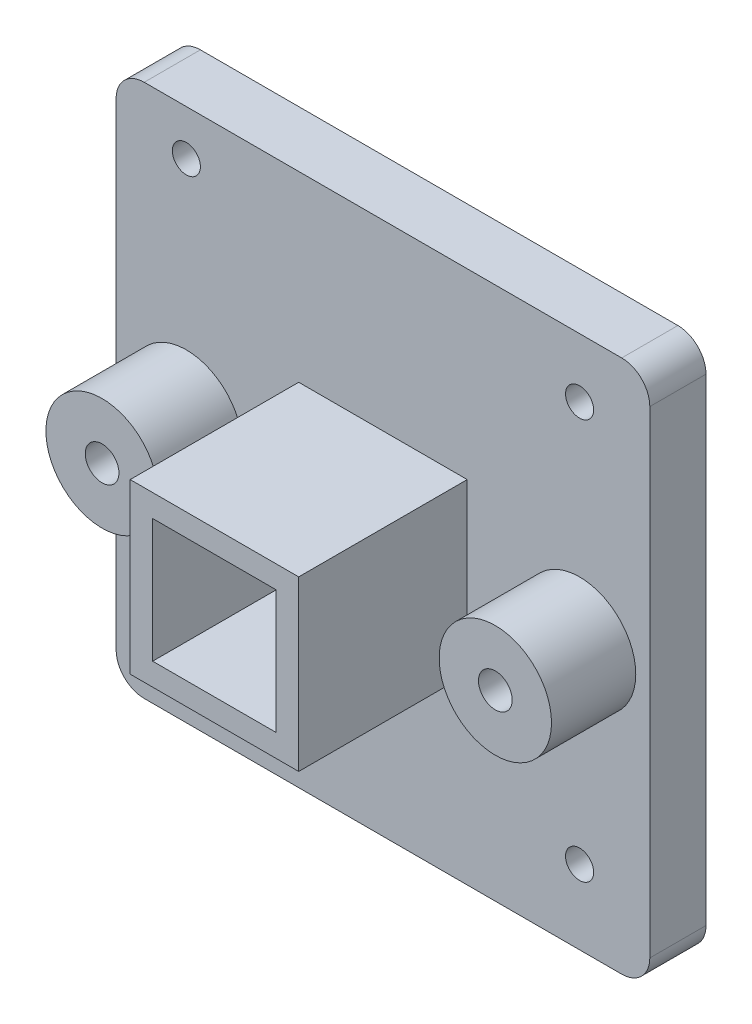
SolidWorks part; units mm, degrees
ref_plane "Front Plane" through (0, 0, 0) normal (0, 0, 1) x (1, 0, 0)
ref_plane "Top Plane" through (0, 0, 0) normal (0, 1, 0) x (1, 0, 0)
ref_plane "Right Plane" through (0, 0, 0) normal (1, 0, 0) x (0, 0, -1)
sketch "Sketch1" plane through (0, 0, 0) normal (0, 0, 1) x (1, 0, 0)
  line L1 (-22, -22) -> (22, -22)
  line L2 (-95, -95) -> (95, -95)
  line L3 (-95, -95) -> (-95, 95)
  line L4 (-95, 95) -> (95, 95)
  line L5 (95, -95) -> (95, 95)
  line L6 (-22, -22) -> (-22, 22)
  line L7 (-22, 22) -> (22, 22)
  line L8 (22, -22) -> (22, 22)
  circle A0 centre (-70, 0) radius 20
  circle A1 centre (70, 0) radius 20
  circle A2 centre (70, -68.5969) radius 5
  circle A3 centre (-70, -73.5969) radius 5
  circle A4 centre (70, 73.9364) radius 5
  circle A5 centre (-70, 78.9364) radius 5
  point P0 (0, 0)
  point P3 (0, 0)
  point P11 (0, 0)
  point P13 (0, 0)
  dimension "D4" = 44
  dimension "D3" = 44
  dimension "D1" = 190
  dimension "D2" = 190
extrude "Boss-Extrude2" add sketch "Sketch1" along normal blind 20
sketch "Sketch2" plane through (0, 0, 0) normal (0, 0, 1) x (1, 0, 0)
  circle A0 centre (-70, 0) radius 20
  circle A1 centre (70, 0) radius 20
  circle A2 centre (-70, 0) radius 6
  circle A3 centre (70, 0) radius 6
extrude "Boss-Extrude5" add sketch "Sketch2" along normal blind 50
sketch "Sketch4" plane through (0, 0, 0) normal (0, 0, 1) x (1, 0, 0)
  circle A0 centre (70, 0) radius 20
  circle A1 centre (-70, 0) radius 20
extrude "Boss-Extrude6" add sketch "Sketch4" along normal blind 3
fillet "Fillet1" radius 10 4 edges at (95, 95, 10) (-95, 95, 10) (-95, -95, 10) (95, -95, 10)
sketch "Sketch6" plane through (0, 0, 0) normal (0, 0, 1) x (1, 0, 0)
  line L0 (22, -22) -> (22, 22) construction
  line L1 (-22, -22) -> (22, -22)
  line L2 (-22, -22) -> (-22, 22)
  line L3 (-22, 22) -> (22, 22)
  line L4 (22, -22) -> (22, 22)
  line L5 (-22, -22) -> (22, 22) construction
  line L6 (-22, 22) -> (22, -22) construction
  line L7 (22, 22) -> (-22, 22) construction
  line L9 (-30, -30) -> (30, -30)
  line L10 (-30, -30) -> (-30, 30)
  line L11 (-30, 30) -> (30, 30)
  line L12 (30, -30) -> (30, 30)
  line L13 (-30, -30) -> (30, 30) construction
  line L14 (-30, 30) -> (30, -30) construction
  point P0 (0, 0)
  point P10 (0, 0)
  dimension "D1" = 60
  dimension "D2" = 60
extrude "Boss-Extrude7" add sketch "Sketch6" along normal blind 80
sketch "Sketch7" plane through (0, 0, 0) normal (0, 0, 1) x (1, 0, 0)
  point P1 (0, 0)
